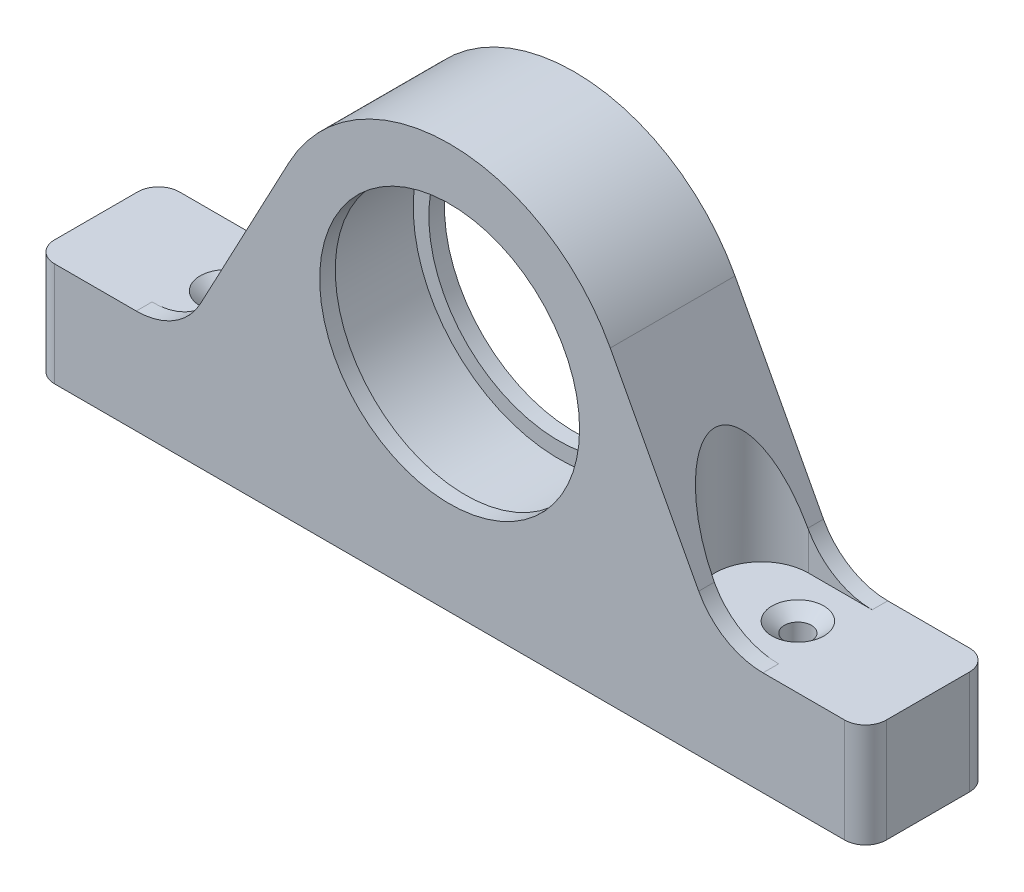
SolidWorks part; units mm, degrees
material "Alloy Steel"
ref_plane "Front Plane" through (0, 0, 0) normal (0, 0, 1) x (1, 0, 0)
ref_plane "Top Plane" through (0, 0, 0) normal (0, 1, 0) x (1, 0, 0)
ref_plane "Right Plane" through (0, 0, 0) normal (1, 0, 0) x (0, 0, -1)
sketch "Sketch1" plane through (0, 0, 0) normal (0, 0, 1) x (1, 0, 0)
  line L0 (-101.6, -54.61) -> (101.6, -54.61)
  line L1 (101.6, -54.61) -> (101.6, -29.21)
  line L2 (101.6, -29.21) -> (76.5573, -29.21)
  line L3 (-101.6, -54.61) -> (-101.6, -29.21)
  line L4 (-101.6, -29.21) -> (-76.5573, -29.21)
  line L5 (-39.247, 20.868) -> (-60.8585, -19.7772)
  line L6 (39.247, 20.868) -> (60.8585, -19.7772)
  circle A0 centre (0, 0) radius 31.75
  arc A1 (-39.247, 20.868) -> (39.247, 20.868) centre (0, 0) cw
  arc A2 (-60.8585, -19.7772) -> (-76.5573, -29.21) centre (-76.5573, -11.43) cw
  arc A4 (60.8585, -19.7772) -> (76.5573, -29.21) centre (76.5573, -11.43) ccw
  point P12 (0, 44.45)
  point P15 (0, -54.61)
  dimension "D3" = 63.5
  dimension "D5" = 44.45
  dimension "D6" = 17.78
  dimension "D7" = 54.61
  dimension "D1" = 25.4
  dimension "D2" = 203.2
  dimension "D4" = 56
extrude "Boss-Extrude1" add sketch "Sketch1" along normal mid plane 30.48
fillet "Fillet1" radius 5.08 4 edges at (101.6, -41.91, -15.24) (101.6, -41.91, 15.24) (-101.6, -41.91, -15.24) (-101.6, -41.91, 15.24)
sketch "Sketch2" plane through (0, -29.21, 0) normal (0, 1, 0) x (1, 0, 0)
  line L0 (0, 117.0308) -> (0, -133.7813) construction
  line L1 (-93.98, 11.43) -> (-60.96, 11.43)
  line L2 (-93.98, -11.43) -> (-60.96, -11.43)
  line L3 (-93.98, 11.43) -> (-93.98, -11.43)
  line L4 (93.98, 11.43) -> (93.98, -11.43)
  line L5 (93.98, -11.43) -> (60.96, -11.43)
  line L6 (93.98, 11.43) -> (60.96, 11.43)
  arc A1 (-60.96, 11.43) -> (-60.96, -11.43) centre (-60.96, 0) cw
  arc A2 (60.96, 11.43) -> (60.96, -11.43) centre (60.96, 0) ccw
  dimension "D2" = 11.43
  dimension "D1" = 22.86
  dimension "D3" = 60.96
  dimension "D4" = 33.02
extrude "Cut-Extrude2" cut sketch "Sketch2" along normal through all
hole_wizard "1/4 (0.26) Diameter Hole1" positions "Sketch3" profile "Sketch4" hole size "1/4" standard "ANSI Inch" end condition up to next
sketch "Sketch3" plane through (0, -29.21, 0) normal (0, 1, 0) x (1, 0, 0)
  line L0 (-101.6, -10.16) -> (-101.6, 10.16) construction
  line L1 (101.6, -10.16) -> (101.6, 10.16) construction
  line L2 (-76.5573, -15.24) -> (-96.52, -15.24) construction
  line L3 (96.52, -15.24) -> (76.5573, -15.24) construction
  point P0 (-69.85, 0)
  point P2 (69.85, 0)
  dimension "D1" = 31.75
  dimension "D2" = 31.75
  dimension "D3" = 15.24
  dimension "D4" = 15.24
sketch "Sketch4" plane through (-69.85, -29.21, 0) normal (1, 0, 0) x (0, 0, 1)
  line L0 (0, 0) -> (0, 25.4)
  line L1 (0, 25.4) -> (3.302, 25.4)
  line L2 (3.302, 25.4) -> (3.302, 2.5576)
  line L3 (3.302, 2.5576) -> (6.35, 0)
  line L5 (6.35, 0) -> (0, 0)
  line L6 (-3.302, 2.5576) -> (-6.35, 0) construction
  line L11 (0, -6.35) -> (0, 107.95) construction
  dimension "Thru Hole Dia." = 6.604
  dimension "Thru Hole Depth" = 25.4
  dimension "Near C'Sink Dia." = 12.7
  dimension "Near C'Sink Angle" = 100
sketch "Sketch5" plane through (0, 0, 0) normal (0, 0, 1) x (1, 0, 0)
  circle A0 centre (0, 0) radius 35.56
  dimension "D1" = 71.12
extrude "Cut-Extrude3" cut sketch "Sketch5" against normal mid plane 22.86
